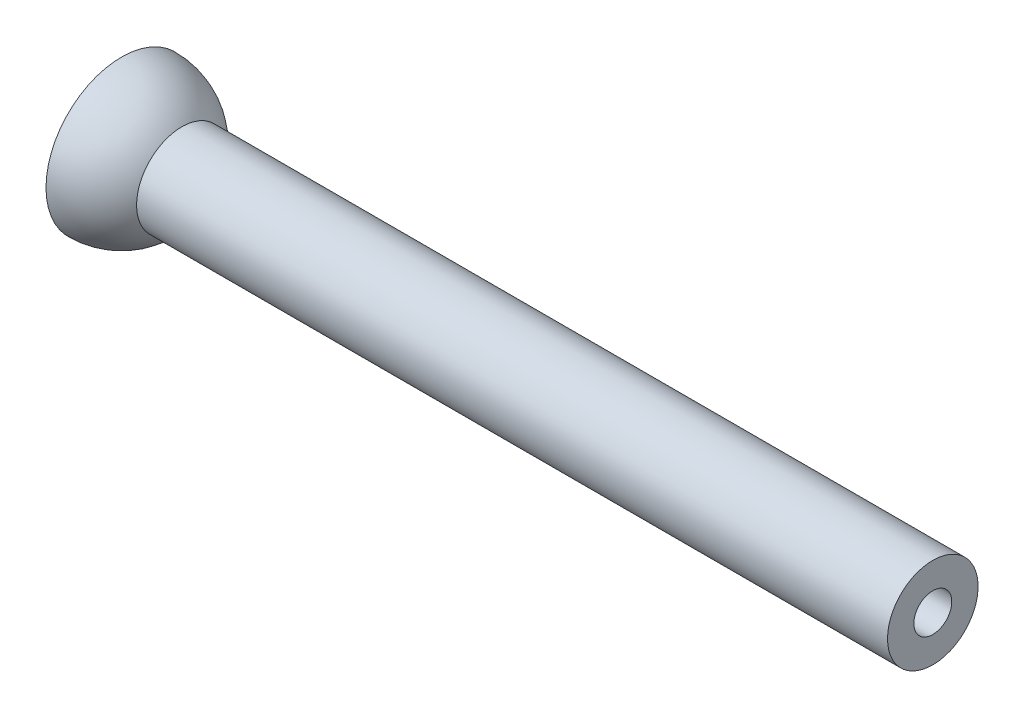
SolidWorks part; units mm, degrees
ref_plane "Front Plane" through (0, 0, 0) normal (0, 0, 1) x (1, 0, 0)
ref_plane "Top Plane" through (0, 0, 0) normal (0, 1, 0) x (1, 0, 0)
ref_plane "Right Plane" through (0, 0, 0) normal (1, 0, 0) x (0, 0, -1)
sketch "Sketch1" plane through (0, 0, 0) normal (0, 1, 0) x (1, 0, 0)
  line L0 (0, 0) -> (17.5462, 0) construction
  line L1 (0, 12.7) -> (0, 10.795)
  line L2 (10.16, 7.62) -> (136.525, 7.62)
  line L3 (10.795, 0) -> (12.7, 0)
  line L4 (12.292, 3.1933) -> (136.525, 3.1933)
  line L5 (136.525, 7.62) -> (136.525, 3.1933)
  arc A0 (10.795, 0) -> (0, 10.795) centre (0, 0) ccw
  arc A1 (12.7, 0) -> (12.292, 3.1933) centre (0, 0) ccw
  arc A2 (10.16, 7.62) -> (0, 12.7) centre (0, 0) ccw
  point P6 (0, 0)
  dimension "D1" = 25.4
  dimension "D2" = 21.59
  dimension "D3" = 136.525
  dimension "D4" = 7.62
revolve "Revolve1" add sketch "Sketch1" angle 360 about L0
